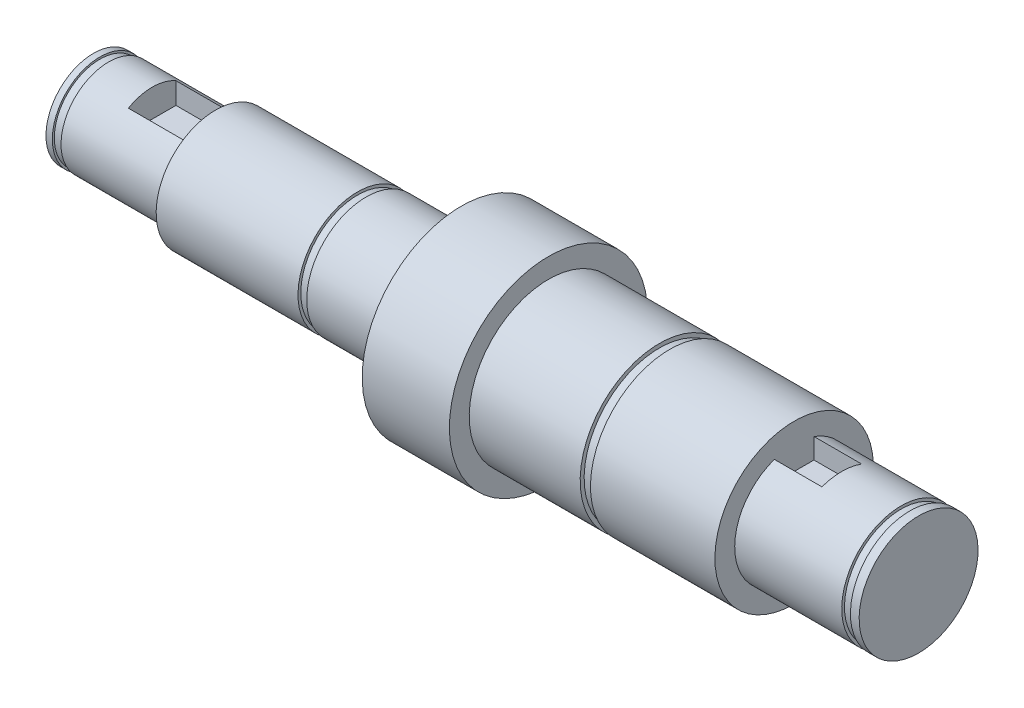
SolidWorks part; units mm, degrees
ref_plane "Front Plane" through (0, 0, 0) normal (0, 0, 1) x (1, 0, 0)
ref_plane "Top Plane" through (0, 0, 0) normal (0, 1, 0) x (1, 0, 0)
ref_plane "Right Plane" through (0, 0, 0) normal (1, 0, 0) x (0, 0, -1)
sketch "Sketch1" plane through (0, 0, 0) normal (0, 0, 1) x (1, 0, 0)
  line L0 (-52.05, 0) -> (52.05, 0)
  line L17 (-52.05, 0) -> (-52.05, 6)
  line L18 (-52.05, 6) -> (-51.25, 6)
  line L19 (-36.65, 6) -> (-36.65, 7.5)
  line L20 (-36.65, 7.5) -> (-18.75, 7.5)
  line L22 (-5.65, 7.5) -> (-5.65, 12.5)
  line L23 (-5.65, 12.5) -> (5.35, 12.5)
  line L24 (5.35, 12.5) -> (5.35, 10)
  line L25 (5.35, 10) -> (19.35, 10)
  line L26 (36.35, 10) -> (36.35, 7.5)
  line L27 (36.35, 7.5) -> (49.85, 7.5)
  line L28 (52.05, 7.5) -> (52.05, 0)
  line L29 (-50.15, 6) -> (-36.65, 6)
  line L31 (-51.25, 6) -> (-51.25, 5.75)
  line L32 (-51.25, 5.75) -> (-50.15, 5.75)
  line L33 (-50.15, 6) -> (-50.15, 5.75)
  line L34 (50.95, 7.5) -> (52.05, 7.5)
  line L36 (49.85, 7.5) -> (49.85, 7.15)
  line L37 (49.85, 7.15) -> (50.95, 7.15)
  line L38 (50.95, 7.5) -> (50.95, 7.15)
  line L39 (-17.65, 7.5) -> (-5.65, 7.5)
  line L41 (-18.75, 7.5) -> (-18.75, 7.15)
  line L42 (-18.75, 7.15) -> (-17.65, 7.15)
  line L43 (-17.65, 7.5) -> (-17.65, 7.15)
  line L44 (20.65, 10) -> (36.35, 10)
  line L46 (19.35, 10) -> (19.35, 9.5)
  line L47 (19.35, 9.5) -> (20.65, 9.5)
  line L48 (20.65, 10) -> (20.65, 9.5)
  point P4 (0, 0)
  point P30 (20.65, 9.75)
  dimension "D1" = 104.1
  dimension "D2" = 6
  dimension "D3" = 7.5
  dimension "D4" = 12.5
  dimension "D5" = 10
  dimension "D6" = 7.5
  dimension "D7" = 15.4
  dimension "D8" = 31
  dimension "D9" = 11
  dimension "D10" = 31
  dimension "D11" = 15.7
  dimension "D12" = 1.1
  dimension "D13" = 0.8
  dimension "D14" = 0.25
  dimension "D15" = 1.1
  dimension "D16" = 1.1
  dimension "D17" = 0.35
  dimension "D18" = 12
  dimension "D19" = 1.1
  dimension "D20" = 0.35
  dimension "D21" = 14
  dimension "D22" = 1.3
  dimension "D23" = 0.5
revolve "Revolve1" add sketch "Sketch1" angle 360 about L0
sketch "Sketch3" plane through (-36.65, 0, 0) normal (-1, 0, 0) x (0, 0, 1)
  line L0 (0, 0) -> (0, 6) construction
  line L1 (-3, 2.5) -> (3, 2.5)
  line L2 (-3, 2.5) -> (-3, 6)
  line L3 (-3, 6) -> (3, 6)
  line L4 (3, 2.5) -> (3, 6)
  circle A0 centre (0, 0) radius 6 construction
  dimension "D1" = 3.5
  dimension "D2" = 6
extrude "Cut-Extrude1" cut sketch "Sketch3" along normal blind 8
sketch "Sketch4" plane through (36.35, 0, 0) normal (1, 0, 0) x (0, 0, -1)
  line L0 (0, 7.5) -> (0, 0) construction
  line L1 (-2.5, 7.5) -> (2.5, 7.5)
  line L2 (-2.5, 7.5) -> (-2.5, 4.5)
  line L3 (-2.5, 4.5) -> (2.5, 4.5)
  line L4 (2.5, 7.5) -> (2.5, 4.5)
  circle A0 centre (0, 0) radius 7.5 construction
  dimension "D1" = 5
  dimension "D2" = 3
extrude "Cut-Extrude3" cut sketch "Sketch4" along normal blind 6
